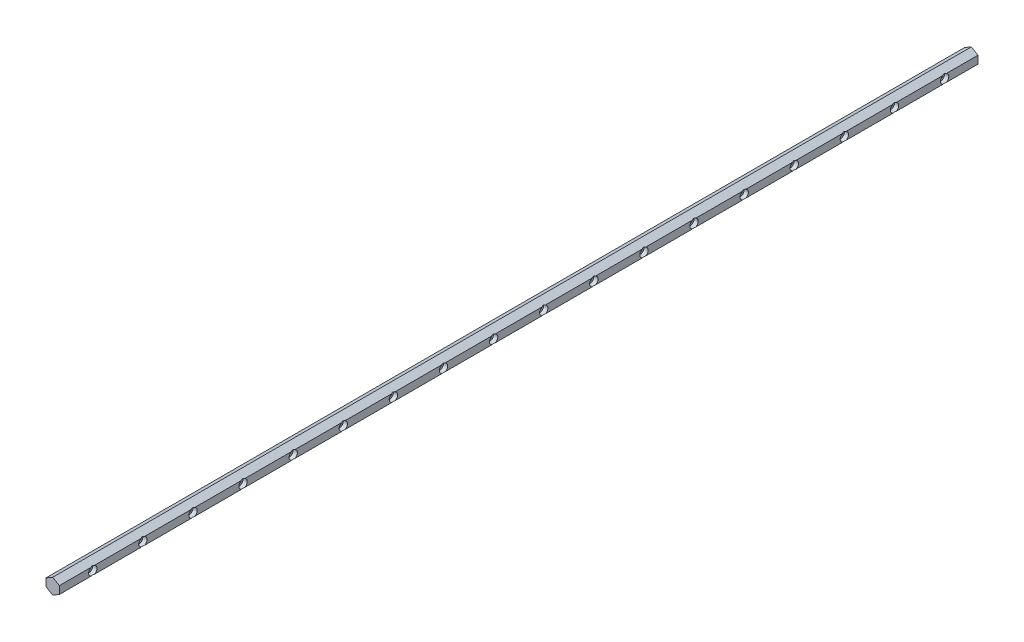
SolidWorks part; units mm, degrees
material "Plain Carbon Steel"
ref_plane "Front Plane" through (0, 0, 0) normal (0, 0, 1) x (1, 0, 0)
ref_plane "Top Plane" through (0, 0, 0) normal (0, 1, 0) x (1, 0, 0)
ref_plane "Right Plane" through (0, 0, 0) normal (1, 0, 0) x (0, 0, -1)
sketch "Sketch1" plane through (0, 0, 0) normal (0, 0, 1) x (1, 0, 0)
  line L1 (0, -9.2376) -> (8, -4.6188)
  line L2 (8, -4.6188) -> (8, 4.6188)
  line L3 (8, 4.6188) -> (0, 9.2376)
  line L4 (0, 9.2376) -> (-8, 4.6188)
  line L5 (-8, 4.6188) -> (-8, -4.6188)
  line L6 (-8, -4.6188) -> (0, -9.2376)
  circle A0 centre (0, 0) radius 8 construction
  dimension "16" = 16
extrude "Boss-Extrude1" add sketch "Sketch1" along normal blind 1100
sketch "Sketch2" plane through (8, 0, 0) normal (1, 0, 0) x (0, 0, -1)
  line L0 (-1100, -4.6188) -> (-1100, 4.6188) construction
  line L1 (-1100, 0) -> (0, 0) construction
  point P9 (-1060, 0)
  dimension "D1" = 40
hole_wizard "CBORE for M5 Socket Head Cap Screw1" positions "3DSketch3" profile "Sketch5" counterbore size "M5" standard "IS" end condition through all
sketch3d "3DSketch3"
  point P0 (8, 0, 1060)
sketch "Sketch5" plane through (8, 0, 1060) normal (0, 1, 0) x (0, 0, -1)
  line L0 (0, 0) -> (0, 16)
  line L1 (0, 16) -> (2.75, 16)
  line L3 (2.75, 16) -> (2.75, 5)
  line L4 (2.75, 5) -> (5, 5)
  line L5 (5, 5) -> (5, 0)
  line L7 (5, 0) -> (0, 0)
  line L11 (0, -6.35) -> (0, 107.95) construction
  dimension "Thru Hole Dia." = 5.5
  dimension "Thru Hole Depth" = 16
  dimension "C'Bore Dia." = 10
  dimension "C'Bore Depth" = 5
pattern_linear "LPattern1" count 18 spacing 60 along (0, 0, -1) of "CBORE for M5 Socket Head Cap Screw1"
equation "\"rail_length\"=1100"
equation "\"D1@Boss-Extrude1\"=\"rail_length\""
equation "\"holeoffset\"=40"
equation "\"holespacing\"=60"
equation "\"D1@Sketch2\"=\"holeoffset\""
equation "\"D3@LPattern1\"=\"holespacing\""
